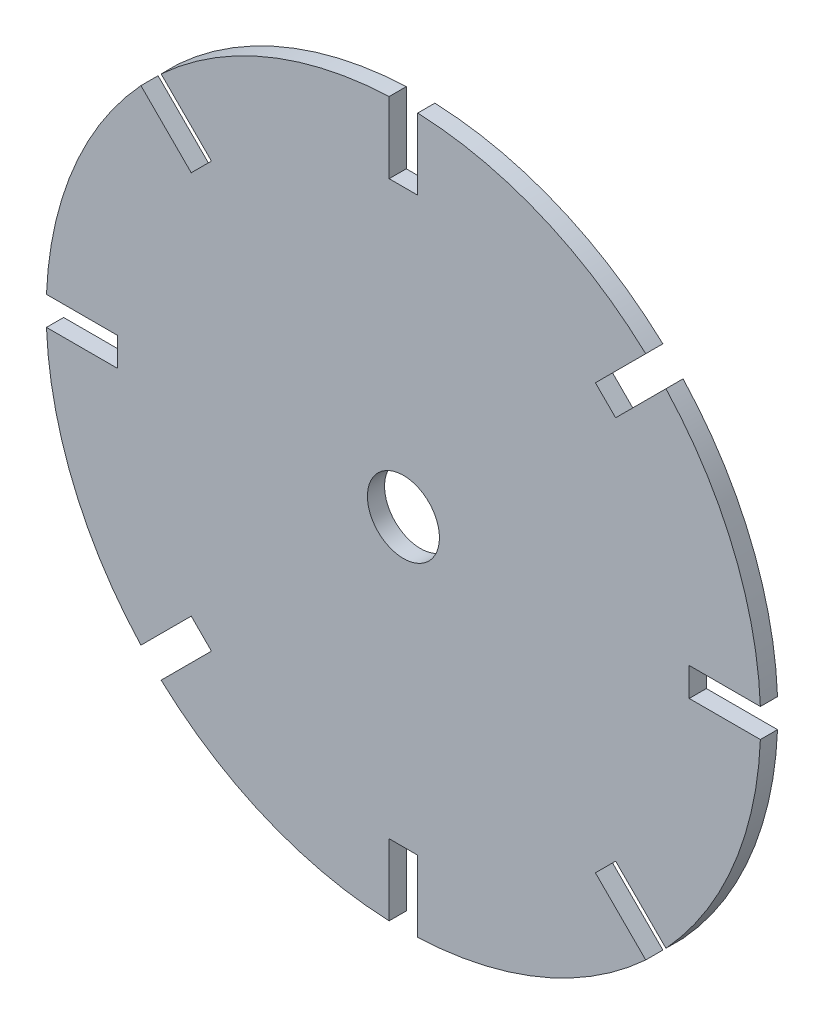
SolidWorks part; units mm, degrees
material "1.0038 (S235JRG2)"
ref_plane "Plan de face" through (0, 0, 0) normal (0, 0, 1) x (1, 0, 0)
ref_plane "Plan de dessus" through (0, 0, 0) normal (0, 1, 0) x (1, 0, 0)
ref_plane "Plan de droite" through (0, 0, 0) normal (1, 0, 0) x (0, 0, -1)
sketch "Esquisse1" plane through (0, 0, 0) normal (0, 0, 1) x (1, 0, 0)
  circle A0 centre (0, 0) radius 125
  circle A1 centre (0, 0) radius 12.6
  point P33 (0, 0)
  dimension "D1" = 25.2
  dimension "D2" = 250
extrude "Boss.-Extru.1" add sketch "Esquisse1" along normal blind 6
sketch "Esquisse2" plane through (0, 0, 0) normal (0, 0, -1) x (-1, 0, 0)
  line L0 (0, 0) -> (0, 125) construction
  line L1 (0, 0) -> (97.7289, 77.9362) construction
  line L2 (0, 0) -> (121.866, -27.8151) construction
  line L3 (0, 0) -> (54.2355, -112.6211) construction
  line L4 (0, 0) -> (-54.2355, -112.6211) construction
  line L5 (0, 0) -> (-121.866, -27.8151) construction
  line L6 (0, 0) -> (-97.7289, 77.9362) construction
  line L8 (-5, 100) -> (5, 100)
  line L9 (-5, 100) -> (-5, 125)
  line L10 (-5, 125) -> (5, 125)
  line L11 (5, 100) -> (5, 125)
  circle A0 centre (0, 0) radius 125 construction
  point P14 (0, 0)
  point P17 (0, 125)
  dimension "D1" = 7
  dimension "D2" = 10
  dimension "D3" = 25
extrude "Enlèv. mat.-Extru.1" cut sketch "Esquisse2" against normal through all
pattern_circular "Répétition circulaire1" count 8 over 360 about axis through (0, 0, 0) along (0, 0, 1) of "Enlèv. mat.-Extru.1"
